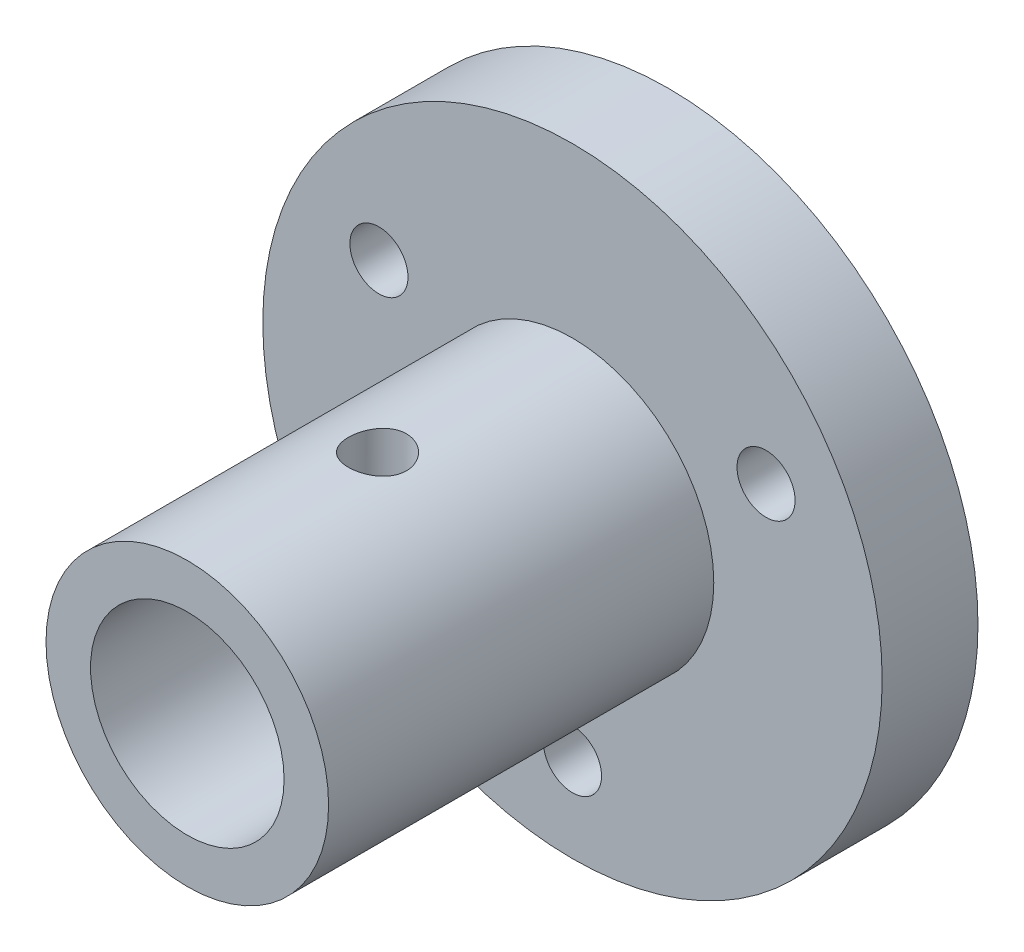
SolidWorks part; units mm, degrees
ref_plane "Front Plane" through (0, 0, 0) normal (0, 0, 1) x (1, 0, 0)
ref_plane "Top Plane" through (0, 0, 0) normal (0, 1, 0) x (1, 0, 0)
ref_plane "Right Plane" through (0, 0, 0) normal (1, 0, 0) x (0, 0, -1)
sketch "Sketch1" plane through (0, 0, 0) normal (0, 0, 1) x (1, 0, 0)
  line L0 (0, 0) -> (0, -23.094) construction
  line L1 (0, 0) -> (20, 11.547) construction
  line L2 (0, 0) -> (-20, 11.547) construction
  line L3 (20, 11.547) -> (0, -23.094) construction
  line L4 (0, -23.094) -> (-20, 11.547) construction
  line L5 (-20, 11.547) -> (20, 11.547) construction
  circle A0 centre (0, 0) radius 32
  circle A1 centre (20, 11.547) radius 3
  circle A2 centre (0, -23.094) radius 3
  circle A3 centre (-20, 11.547) radius 3
  circle A4 centre (0, 0) radius 10 construction
  dimension "D1" = 64
  dimension "D7" = 6
  dimension "D8" = 6
  dimension "D9" = 6
  dimension "D10" = 20
  dimension "D2" = 40
  dimension "D3" = 40
extrude "Boss-Extrude1" add sketch "Sketch1" along normal blind 9.9
sketch "Sketch2" plane through (0, 0, 9.9) normal (0, 0, 1) x (1, 0, 0)
  circle A0 centre (0, 0) radius 10
  circle A1 centre (0, 0) radius 14.6
  dimension "D1" = 20
  dimension "D2" = 4.6
extrude "Boss-Extrude2" add sketch "Sketch2" along normal blind 39.8
sketch "Sketch3" plane through (0, 0, 0) normal (0, 1, 0) x (1, 0, 0)
  line L0 (0, -9.9) -> (0, -30.05)
  line L1 (-14.6, -9.9) -> (14.6, -9.9) construction
  circle A0 centre (0, -30.05) radius 3
  dimension "D2" = 6
  dimension "D1" = 20.15
extrude "Cut-Extrude1" cut sketch "Sketch3" against normal through all both and the other way through all
